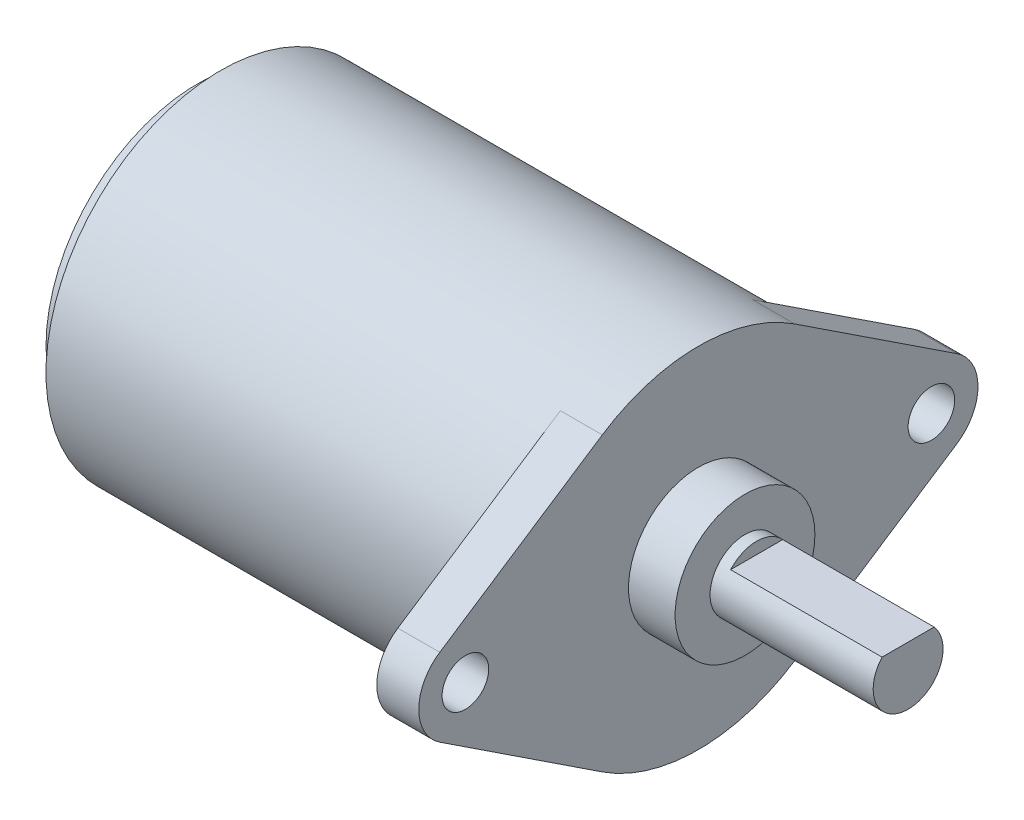
SolidWorks part; units mm, degrees
ref_plane "前视基准面" through (0, 0, 0) normal (0, 0, 1) x (1, 0, 0)
ref_plane "上视基准面" through (0, 0, 0) normal (0, 1, 0) x (1, 0, 0)
ref_plane "右视基准面" through (0, 0, 0) normal (1, 0, 0) x (0, 0, -1)
sketch "草图1" plane through (0, 0, 0) normal (1, 0, 0) x (0, 0, -1)
  circle A0 centre (0, 0) radius 7.5
extrude "凸台-拉伸1" add sketch "草图1" along normal blind 18.7
sketch "草图2" plane through (18.7, 0, 0) normal (1, 0, 0) x (0, 0, -1)
  line L0 (0, 0) -> (50000, 0) construction
  line L1 (4.125, 6.2637) -> (11.1, 1.6703)
  line L2 (0, 0) -> (0, -50000) construction
  line L3 (4.125, -6.2637) -> (11.1, -1.6703)
  line L4 (-4.125, 6.2637) -> (-11.1, 1.6703)
  line L5 (-4.125, -6.2637) -> (-11.1, -1.6703)
  circle A0 centre (10, 0) radius 1
  arc A1 (11.1, -1.6703) -> (11.1, 1.6703) centre (10, 0) ccw
  arc A2 (4.125, 6.2637) -> (-4.125, 6.2637) centre (0, 0) ccw
  arc A3 (-11.1, -1.6703) -> (-11.1, 1.6703) centre (-10, 0) cw
  circle A4 centre (-10, 0) radius 1
  arc A5 (-4.125, -6.2637) -> (4.125, -6.2637) centre (0, 0) ccw
extrude "凸台-拉伸2" add sketch "草图2" along normal blind 1.8
sketch "草图3" plane through (0, 0, 0) normal (-1, 0, 0) x (0, 0, 1)
  circle A0 centre (0, 0) radius 6.5
extrude "凸台-拉伸3" add sketch "草图3" along normal blind 1
sketch "草图4" plane through (-1, 0, 0) normal (-1, 0, 0) x (0, 0, 1)
  circle A0 centre (0, 0) radius 2.7
extrude "凸台-拉伸4" add sketch "草图4" along normal blind 1
sketch "草图5" plane through (-2, 0, 0) normal (-1, 0, 0) x (0, 0, 1)
  circle A0 centre (0, 0) radius 0.75
extrude "凸台-拉伸5" add sketch "草图5" along normal blind 0.5
sketch "草图6" plane through (20.5, 0, 0) normal (1, 0, 0) x (0, 0, -1)
  circle A0 centre (0, 0) radius 3
extrude "凸台-拉伸6" add sketch "草图6" along normal blind 2
sketch "草图7" plane through (22.5, 0, 0) normal (1, 0, 0) x (0, 0, -1)
  circle A0 centre (0, 0) radius 1.5
extrude "凸台-拉伸7" add sketch "草图7" along normal blind 0.5
sketch "草图8" plane through (23, 0, 0) normal (1, 0, 0) x (0, 0, -1)
  line L1 (0, 1) -> (1.118, 1)
  line L2 (0, 1) -> (-1.118, 1)
  arc A0 (-1.118, 1) -> (1.118, 1) centre (0, 0) ccw
extrude "凸台-拉伸8" add sketch "草图8" along normal blind 6.5
